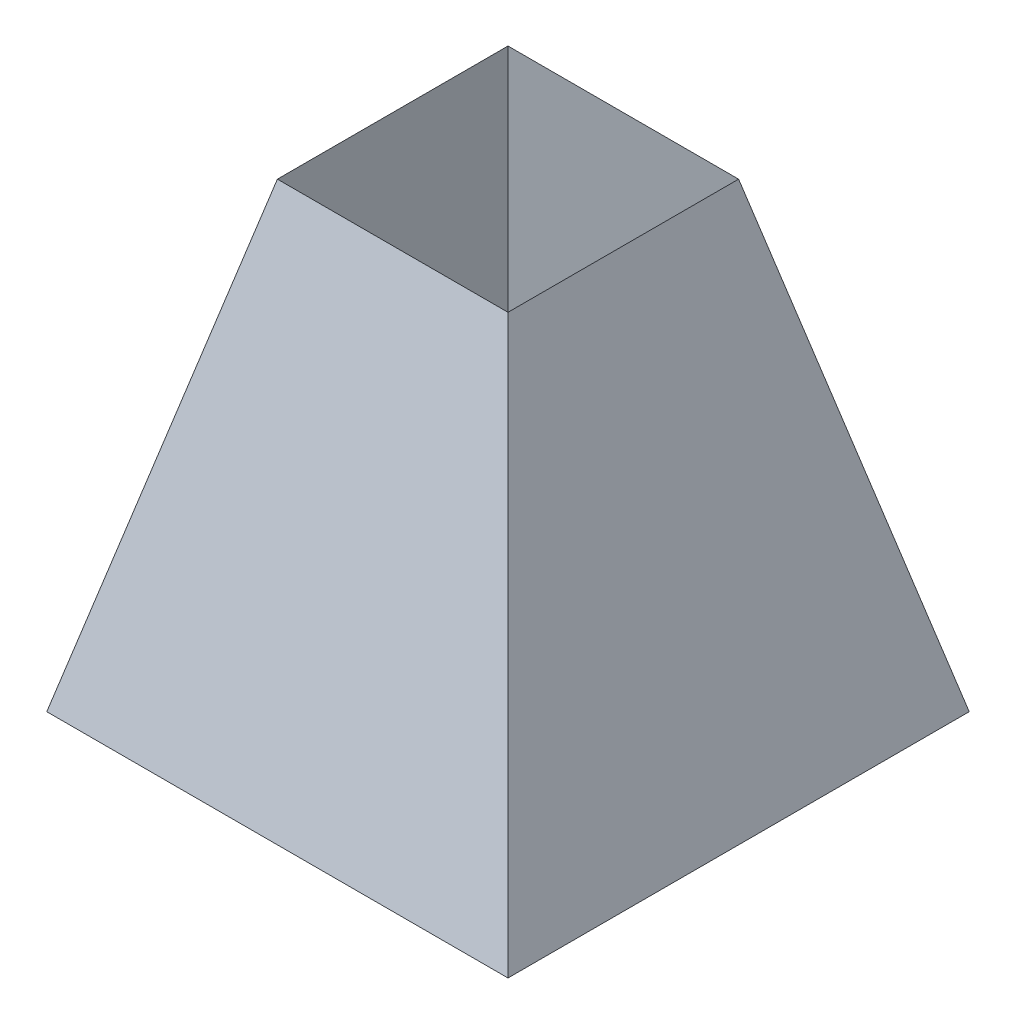
SolidWorks part; units mm, degrees
material "ASTM A36 Steel"
ref_plane "Front Plane" through (0, 0, 0) normal (0, 0, 1) x (1, 0, 0)
ref_plane "Top Plane" through (0, 0, 0) normal (0, 1, 0) x (1, 0, 0)
ref_plane "Right Plane" through (0, 0, 0) normal (1, 0, 0) x (0, 0, -1)
sketch "Sketch1" plane through (0, 0, 0) normal (0, 1, 0) x (1, 0, 0)
  line L1 (-101.6, 101.6) -> (101.6, 101.6)
  line L2 (-101.6, 101.6) -> (-101.6, -101.6)
  line L3 (-101.6, -101.6) -> (101.6, -101.6)
  line L4 (101.6, 101.6) -> (101.6, -101.6)
  line L5 (-101.6, 101.6) -> (101.6, -101.6) construction
  line L6 (-101.6, -101.6) -> (101.6, 101.6) construction
  point P0 (0, 0)
  dimension "D1" = 203.2
  dimension "D2" = 203.2
ref_plane "Top Surface Plane" through (0, 203.2, 0) normal (0, 1, 0) x (1, 0, 0)
sketch "Sketch2" plane through (0, 203.2, 0) normal (0, 1, 0) x (1, 0, 0)
  line L0 (-101.6, 101.6) -> (101.6, -101.6) construction
  line L1 (-50.8, 50.8) -> (50.8, 50.8)
  line L2 (-50.8, 50.8) -> (-50.8, -50.8)
  line L3 (-50.8, -50.8) -> (50.8, -50.8)
  line L4 (50.8, 50.8) -> (50.8, -50.8)
  line L5 (-50.8, 50.8) -> (50.8, -50.8) construction
  line L6 (-50.8, -50.8) -> (50.8, 50.8) construction
  point P0 (0, 0)
  dimension "D1" = 101.6
loft "Loft1" add profiles "Sketch1", "Sketch2"
sketch "Sketch14" plane through (0, 203.2, 0) normal (0, 1, 0) x (1, 0, 0)
  line L0 (50.8, -50.8) -> (50.8, 50.8) construction
  line L1 (-50.8, 50.8) -> (50.8, 50.8)
  line L2 (-50.8, 50.8) -> (-50.8, -50.8)
  line L3 (-50.8, -50.8) -> (50.8, -50.8)
  line L4 (50.8, 50.8) -> (50.8, -50.8)
  line L5 (-50.8, 50.8) -> (50.8, -50.8) construction
  line L6 (-50.8, -50.8) -> (50.8, 50.8) construction
  line L7 (-50.8, -50.8) -> (50.8, -50.8) construction
  point P0 (0, 0)
extrude "Cut-Extrude2" cut sketch "Sketch14" against normal blind 203.2 draft 8 draft outward yes
